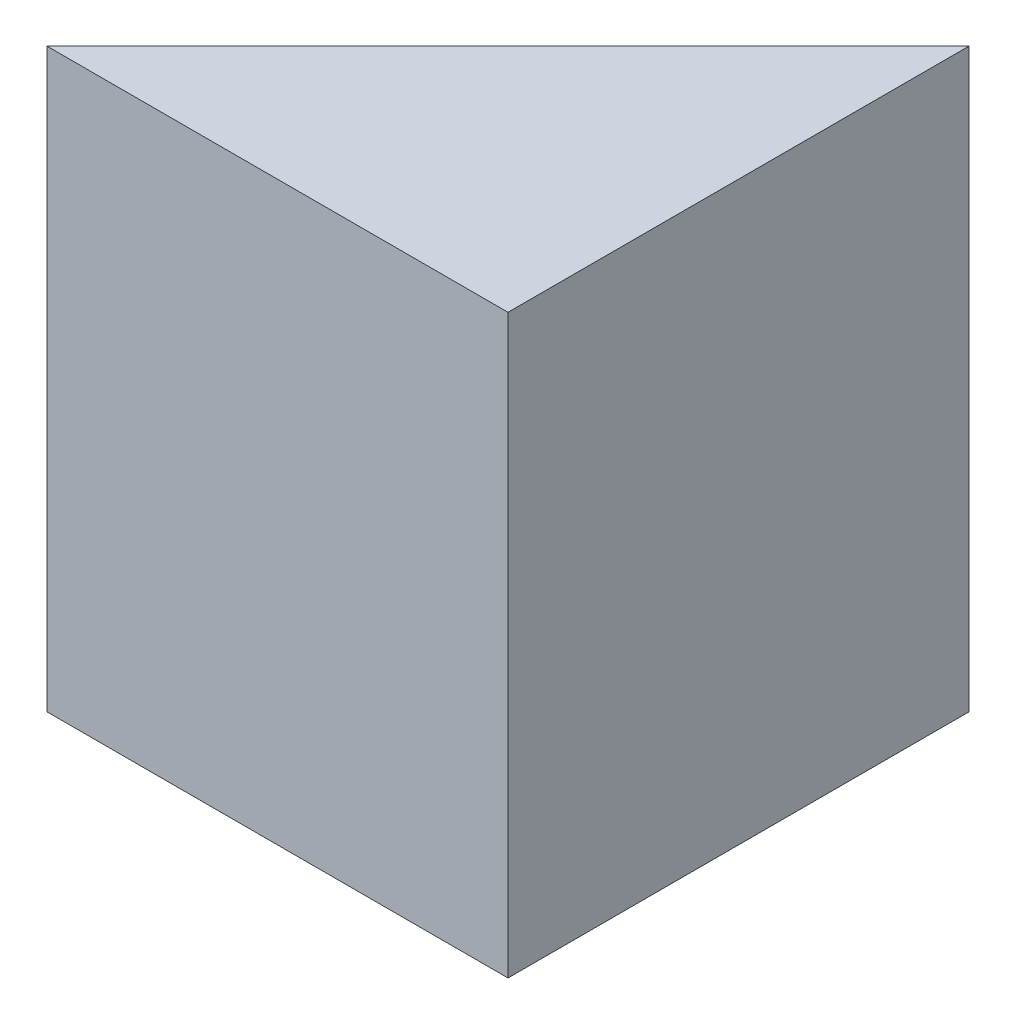
SolidWorks part; units mm, degrees
ref_plane "Front Plane" through (0, 0, 0) normal (0, 0, 1) x (1, 0, 0)
ref_plane "Top Plane" through (0, 0, 0) normal (0, 1, 0) x (1, 0, 0)
ref_plane "Right Plane" through (0, 0, 0) normal (1, 0, 0) x (0, 0, -1)
sketch "Sketch1" plane through (0, 0, 0) normal (0, 1, 0) x (1, 0, 0)
  line L0 (0, 0) -> (40, 0)
  line L1 (40, 0) -> (40, 40)
  line L2 (40, 40) -> (0, 0)
  dimension "D1" = 40
  dimension "D2" = 40
extrude "Boss-Extrude1" add sketch "Sketch1" along normal blind 50
